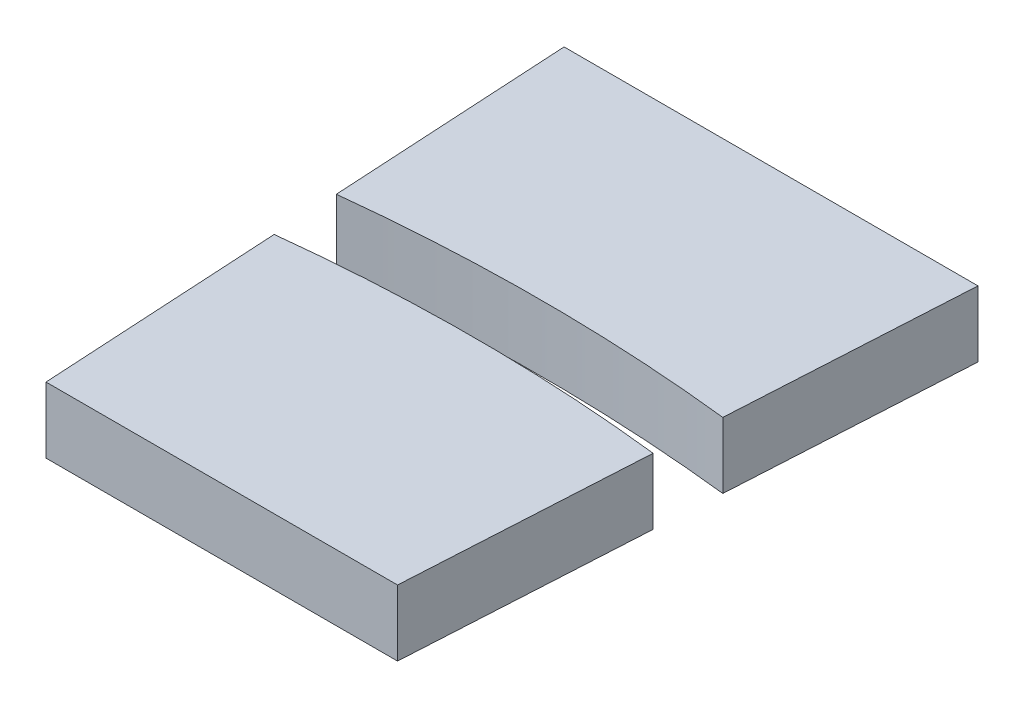
SolidWorks part; units mm, degrees
ref_plane "Front Plane" through (0, 0, 0) normal (0, 0, 1) x (1, 0, 0)
ref_plane "Top Plane" through (0, 0, 0) normal (0, 1, 0) x (1, 0, 0)
ref_plane "Right Plane" through (0, 0, 0) normal (1, 0, 0) x (0, 0, -1)
sketch "Sketch1" plane through (0, 0, 0) normal (0, 1, 0) x (1, 0, 0)
  line L0 (-9.4196, 89.5) -> (-8, 64.5)
  line L5 (-9.4196, 89.5) -> (0, 89.5)
  line L6 (0, 89.5) -> (0, 64.5)
  line L7 (0, 64.5) -> (-8, 64.5)
  point P4 (0, 77)
  dimension "D1" = 25
  dimension "D2" = 77
  dimension "D3" = 3.25
  dimension "D4" = 8
extrude "Boss-Extrude1" add sketch "Sketch1" along normal blind 3
mirror "Mirror1" about plane through (0, 0, 0) normal (1, 0, 0) of "Boss-Extrude1"
sketch "Sketch2" plane through (0, 3, 0) normal (0, 1, 0) x (1, 0, 0)
  line L0 (-9.4196, 89.5) -> (-8, 64.5) construction
  line L1 (9.4196, 89.5) -> (8, 64.5) construction
  line L2 (-8.6251, 75.509) -> (-8.7955, 78.5089)
  line L3 (8.7955, 78.5089) -> (8.6251, 75.509)
  arc A0 (-8.7955, 78.5089) -> (8.7955, 78.5089) centre (0, 0) cw
  arc A1 (-8.6251, 75.509) -> (8.6251, 75.509) centre (0, 0) cw
  dimension "D1" = 79
  dimension "D2" = 76
extrude "Cut-Extrude1" cut sketch "Sketch2" against normal through all both and the other way through all
